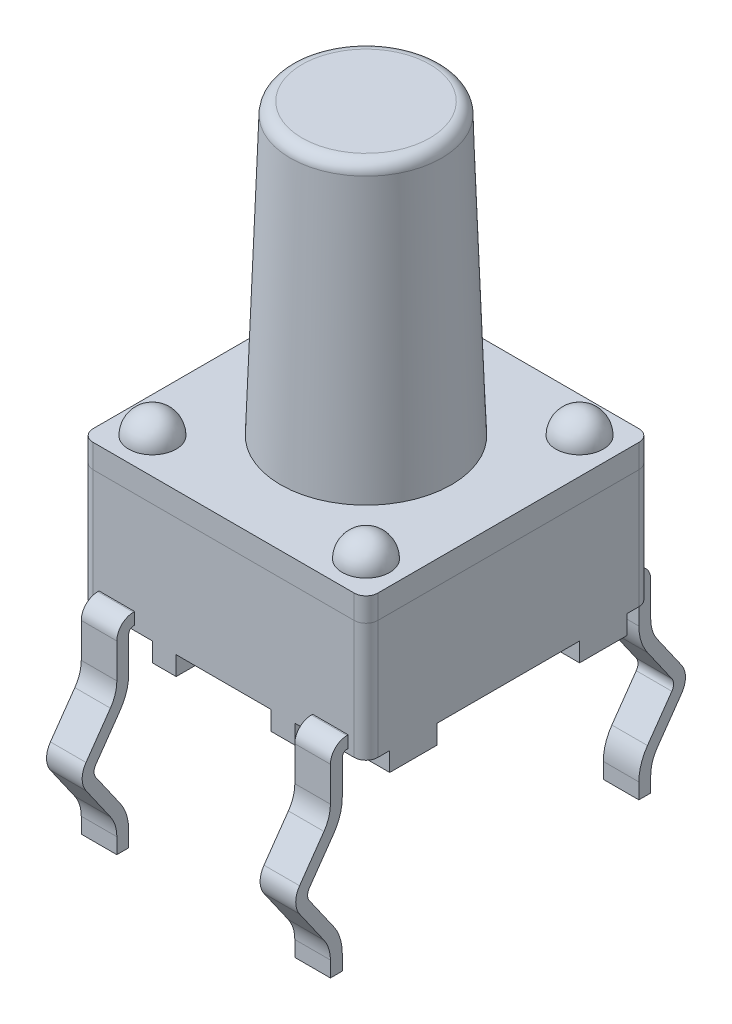
SolidWorks part; units mm, degrees
ref_plane "Front Plane" through (0, 0, 0) normal (0, 0, 1) x (1, 0, 0)
ref_plane "Top Plane" through (0, 0, 0) normal (0, 1, 0) x (1, 0, 0)
ref_plane "Right Plane" through (0, 0, 0) normal (1, 0, 0) x (0, 0, -1)
sketch "Sketch1" plane through (0, 0, 0) normal (0, 1, 0) x (1, 0, 0)
  line L1 (-3, -3) -> (3, -3)
  line L2 (-3, -3) -> (-3, 3)
  line L3 (-3, 3) -> (3, 3)
  line L4 (3, -3) -> (3, 3)
  line L5 (-3, -3) -> (3, 3) construction
  line L6 (-3, 3) -> (3, -3) construction
  point P0 (0, 0)
  dimension "D1" = 6
  dimension "D2" = 6
extrude "Extrude1" add sketch "Sketch1" along normal blind 3.4
sketch "Sketch2" plane through (0, 0, 0) normal (0, -1, 0) x (1, 0, 0)
  line L0 (-3, -3) -> (-3, 3) construction
  line L1 (-3, 1.5) -> (-1.5, 1.5)
  line L2 (-3, 1.5) -> (-3, -1.5)
  line L3 (-3, -1.5) -> (-1.5, -1.5)
  line L4 (-1.5, 1.5) -> (-1.5, -1.5)
  line L5 (3, -3) -> (-3, -3) construction
  line L6 (-3, -2.5) -> (-1.5, -2.5)
  line L7 (-3, -2.5) -> (-3, -3)
  line L8 (-3, -3) -> (-1.5, -3)
  line L9 (-1.5, -2.5) -> (-1.5, -3)
  line L10 (-3, 3) -> (3, 3) construction
  line L11 (-3, 3) -> (-1.5, 3)
  line L12 (-3, 3) -> (-3, 2.5)
  line L13 (-3, 2.5) -> (-1.5, 2.5)
  line L14 (-1.5, 3) -> (-1.5, 2.5)
  line L15 (1, 3) -> (-1, 3)
  line L16 (0, 3) -> (0, -3) construction
  line L17 (1, -3) -> (-1, -3)
  line L18 (-1, 3) -> (-1, -3)
  line L19 (0.5, -2) -> (0.5, -2.5)
  line L20 (0.5, 2.5) -> (-0.5, 2.5)
  line L21 (0.5, 0.25) -> (0.5, -0.25)
  line L22 (0.5, 2) -> (-0.5, 2)
  line L23 (-0.5, 2.5) -> (-0.5, 2)
  line L24 (0.5, 0.25) -> (-0.5, 0.25)
  line L25 (0.5, 2.5) -> (0.5, 2)
  line L26 (0.5, -0.25) -> (-0.5, -0.25)
  line L27 (-0.5, 0.25) -> (-0.5, -0.25)
  line L28 (0.5, -2) -> (-0.5, -2)
  line L29 (1, 3) -> (1, -3)
  line L30 (0.5, -2.5) -> (-0.5, -2.5)
  line L31 (-0.5, -2) -> (-0.5, -2.5)
  line L32 (1.5, 3) -> (1.5, 2.5)
  line L33 (3, 2.5) -> (1.5, 2.5)
  line L34 (3, 3) -> (3, 2.5)
  line L35 (3, 3) -> (1.5, 3)
  line L36 (1.5, -2.5) -> (1.5, -3)
  line L37 (3, -3) -> (1.5, -3)
  line L38 (3, -2.5) -> (3, -3)
  line L39 (3, -2.5) -> (1.5, -2.5)
  line L40 (1.5, 1.5) -> (1.5, -1.5)
  line L41 (3, -1.5) -> (1.5, -1.5)
  line L42 (3, 1.5) -> (3, -1.5)
  line L43 (3, 1.5) -> (1.5, 1.5)
  point P25 (0, 2.5)
  point P29 (0, 0.25)
  point P33 (0, -2)
  point P40 (0, -2.5)
  point P42 (0, -0.25)
  point P44 (0, 2)
  dimension "D1" = 3
  dimension "D2" = 1.5
  dimension "D3" = 0.5
  dimension "D4" = 1.5
  dimension "D5" = 1
  dimension "D6" = 0.5
  dimension "D7" = 0.5
  dimension "D8" = 0.25
extrude "Extrude2" cut sketch "Sketch2" against normal blind 0.4
sketch "Sketch3" plane through (0, 3.4, 0) normal (0, 1, 0) x (1, 0, 0)
  line L0 (-2.25, 1.75) -> (-2.25, 2.75)
  arc A0 (-2.25, 2.75) -> (-2.25, 1.75) centre (-2.25, 2.25) ccw
  dimension "D3" = 1
  dimension "D1" = 2.25
  dimension "D2" = 2.25
revolve "Revolve1" add sketch "Sketch3" angle 180 about L0
pattern_linear "LPattern1" count 2 spacing 4.5 along (1, 0, 0) count 2 spacing 4.5 along (0, 0, 1) of "Revolve1"
sketch "Sketch4" plane through (0, 3.4, 0) normal (0, 1, 0) x (1, 0, 0)
  circle A0 centre (0, 0) radius 1.8
  dimension "D1" = 3.6
extrude "Extrude3" add sketch "Sketch4" along normal blind 6.1 draft 2
ref_plane "Plane1" through (2.25, 0, 0) normal (1, 0, 0) x (0, 0, -1)
sketch "Sketch5" plane through (2.25, 0, 0) normal (1, 0, 0) x (0, 0, -1)
  line L0 (3.125, -3.5) -> (3.125, -3.1721)
  line L1 (3.3058, -2.5985) -> (3.8197, -1.8647)
  line L2 (3.8197, -1.6353) -> (3.3058, -0.9015)
  line L3 (3.125, -0.3279) -> (3.125, 0.4)
  line L4 (3.025, 0.5) -> (3, 0.5)
  line L5 (3, 3.4) -> (3, 0.4) construction
  line L6 (3.375, -3.5) -> (3.375, -3.1721)
  line L7 (3.5106, -2.7419) -> (4.0245, -2.0081)
  line L8 (4.0245, -1.4919) -> (3.5106, -0.7581)
  line L9 (3.375, -0.3279) -> (3.375, 0.4)
  line L10 (3.025, 0.75) -> (3, 0.75)
  line L11 (3, 0.75) -> (3, 0.5)
  line L12 (3.125, -3.5) -> (3.375, -3.5)
  arc A0 (3.3058, -0.9015) -> (3.125, -0.3279) centre (4.125, -0.3279) cw
  arc A1 (3.125, -3.1721) -> (3.3058, -2.5985) centre (4.125, -3.1721) cw
  arc A2 (3.8197, -1.8647) -> (3.8197, -1.6353) centre (3.6558, -1.75) ccw
  arc A3 (3.125, 0.4) -> (3.025, 0.5) centre (3.025, 0.4) ccw
  arc A4 (3.375, -3.1721) -> (3.5106, -2.7419) centre (4.125, -3.1721) cw
  arc A5 (4.0245, -2.0081) -> (4.0245, -1.4919) centre (3.6558, -1.75) ccw
  arc A6 (3.5106, -0.7581) -> (3.375, -0.3279) centre (4.125, -0.3279) cw
  arc A7 (3.375, 0.4) -> (3.025, 0.75) centre (3.025, 0.4) ccw
  point P16 (3.9, -1.75)
  dimension "D7" = 1
  dimension "D9" = 0.2
  dimension "D10" = 0.1
  dimension "D1" = 3.5
  dimension "D2" = 3.9
  dimension "D3" = 3.125
  dimension "D4" = 1.75
  dimension "D5" = 145
  dimension "D6" = 145
  dimension "D8" = 0.5
  dimension "D11" = 0.25
extrude "Extrude4" add sketch "Sketch5" along normal mid plane 0.75
mirror "Mirror1" about plane through (0, 0, 0) normal (0, 0, 1) of "Extrude4"
mirror "Mirror2" about plane through (0, 0, 0) normal (1, 0, 0) of "Extrude4", "Mirror1"
ref_plane "Plane2" through (0, 2.9, 0) normal (0, 1, 0) x (-1, 0, 0)
split line "Split Line1"
fillet "Fillet1" radius 0.25 9 edges at (-3, 3.15, -3) (3, 3.15, -3) (3, 3.15, 3) (-3, 3.15, 3) (-3, 1.65, -3) (3, 1.65, -3) (3, 1.65, 3) (-3, 1.65, 3) (0, 9.5, 1.587)
